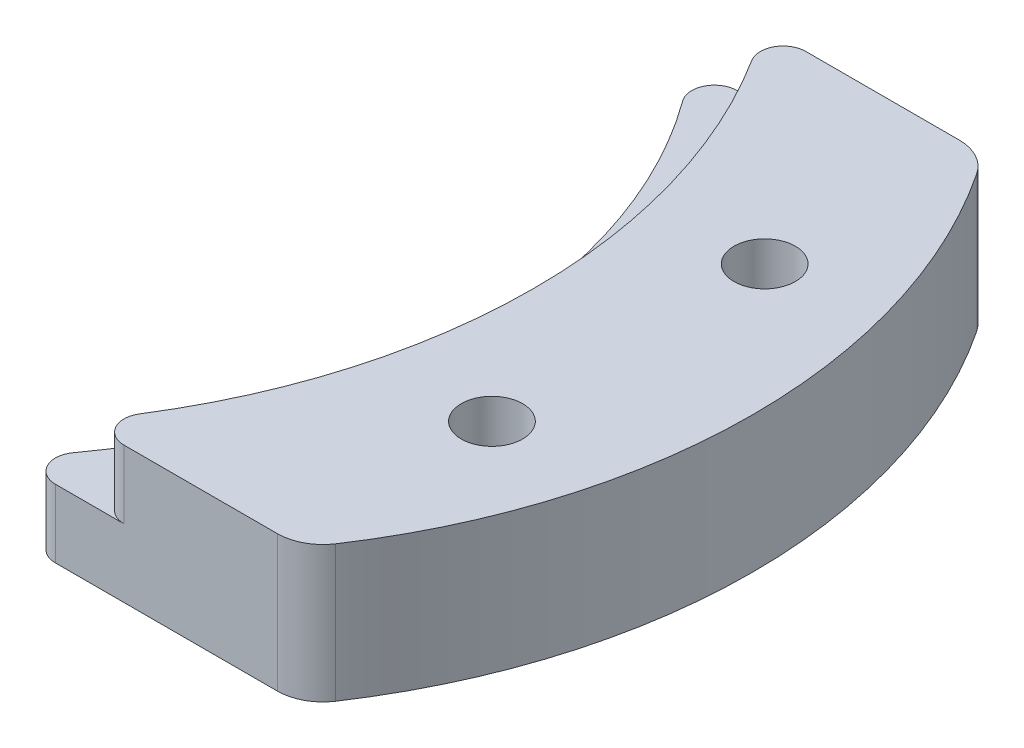
SolidWorks part; units mm, degrees
ref_plane "Спереди" through (0, 0, 0) normal (0, 0, 1) x (1, 0, 0)
ref_plane "Сверху" through (0, 0, 0) normal (0, 1, 0) x (1, 0, 0)
ref_plane "Справа" through (0, 0, 0) normal (1, 0, 0) x (0, 0, -1)
sketch "Эскиз1" plane through (0, 0, 0) normal (0, 1, 0) x (1, 0, 0)
  line L1 (-30, -15) -> (30, -15)
  line L2 (-30, -15) -> (-30, 15) construction
  line L3 (-30, 15) -> (30, 15)
  line L4 (30, -15) -> (30, 15) construction
  line L5 (-30, -15) -> (30, 15) construction
  line L6 (-30, 15) -> (30, -15) construction
  arc A0 (30, 15) -> (30, -15) centre (9.3784, 0) cw
  circle A1 centre (0, 0) radius 22.75
  point P0 (0, 0)
  dimension "D1" = 45.5
  dimension "D2" = 25.5
  dimension "D3" = 60
  dimension "D4" = 30
extrude "Бобышка-Вытянуть1" add sketch "Эскиз1" along normal blind 6 contours A1 L1 A0 L3
sketch "Эскиз2" plane through (0, 6, 0) normal (0, 1, 0) x (1, 0, 0)
  circle A0 centre (0, 0) radius 25.25
  circle A1 centre (0, 0) radius 22.75
  arc A2 (17.1045, -15) -> (17.1045, 15) centre (0, 0) ccw construction
  dimension "D1" = 2.5
extrude "Вырез-Вытянуть1" cut sketch "Эскиз2" against normal blind 3
fillet "Скругление1" radius 1 4 edges at (20.3116, 4.5, -15) (17.1045, 1.5, -15) (20.3116, 4.5, 15) (17.1045, 1.5, 15)
fillet "Скругление2" radius 2 2 edges at (30, 3, -15) (30, 3, 15)
sketch "Эскиз3" plane through (0, 6, 0) normal (0, 1, 0) x (1, 0, 0)
  line L0 (25.25, 0) -> (34.8784, 0) construction
  circle A0 centre (0, 0) radius 30 construction
  arc A1 (21.3591, -13.4667) -> (21.3591, 13.4667) centre (0, 0) ccw construction
  arc A2 (30.6213, -14.1064) -> (30.6213, 14.1064) centre (9.3784, 0) ccw construction
  circle A3 centre (29.3939, 6) radius 1.35
  circle A5 centre (29.3939, -6) radius 1.35
  dimension "D1" = 12
  dimension "D2" = 2.7
  dimension "D3" = 60
extrude "Вырез-Вытянуть2" cut sketch "Эскиз3" against normal through all
chamfer "Фаска1" distance 1.5 angle 45 2 edges at (29.3939, 0, 4.65) (29.3939, 0, -4.65)
